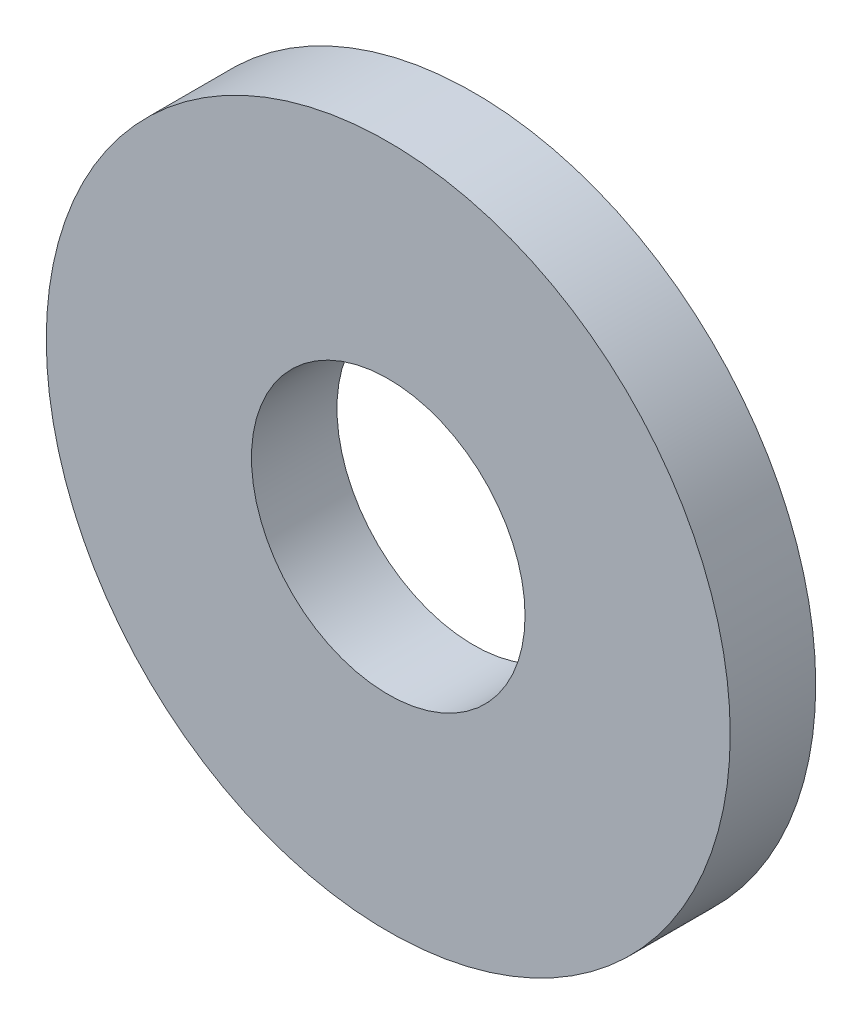
SolidWorks part; units mm, degrees
material "Laiton"
ref_plane "Plan de face" through (0, 0, 0) normal (0, 0, 1) x (1, 0, 0)
ref_plane "Plan de dessus" through (0, 0, 0) normal (0, 1, 0) x (1, 0, 0)
ref_plane "Plan de droite" through (0, 0, 0) normal (1, 0, 0) x (0, 0, -1)
sketch "Esquisse1" plane through (0, 0, 0) normal (0, 0, 1) x (1, 0, 0)
  circle A0 centre (0, 0) radius 1.6
  circle A1 centre (0, 0) radius 4
  dimension "D1" = 8
  dimension "D2" = 3.2
extrude "Extrusion1" add sketch "Esquisse1" along normal blind 1
